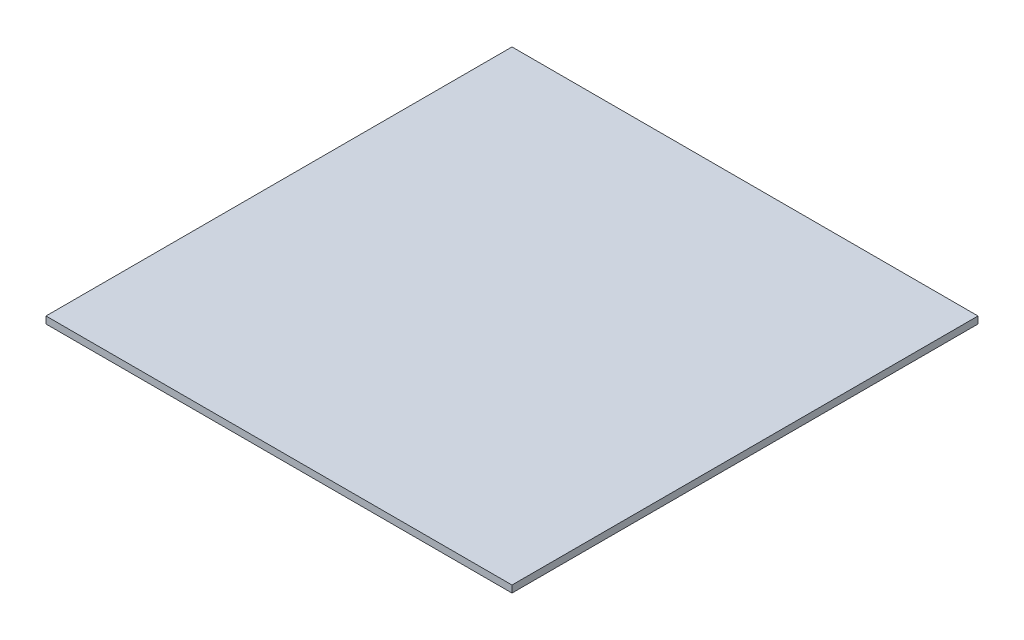
SolidWorks part; units mm, degrees
ref_plane "Front Plane" through (0, 0, 0) normal (0, 0, 1) x (1, 0, 0)
ref_plane "Top Plane" through (0, 0, 0) normal (0, 1, 0) x (1, 0, 0)
ref_plane "Right Plane" through (0, 0, 0) normal (1, 0, 0) x (0, 0, -1)
sketch "Sketch1" plane through (0, 0, 0) normal (0, 1, 0) x (1, 0, 0)
  line L1 (-25.4, -25.4) -> (25.4, -25.4)
  line L2 (-25.4, -25.4) -> (-25.4, 25.4)
  line L3 (-25.4, 25.4) -> (25.4, 25.4)
  line L4 (25.4, -25.4) -> (25.4, 25.4)
  line L5 (-25.4, -25.4) -> (25.4, 25.4) construction
  line L6 (-25.4, 25.4) -> (25.4, -25.4) construction
  point P0 (0, 0)
  dimension "D1" = 50.8
extrude "Boss-Extrude1" add sketch "Sketch1" along normal blind 0.762
